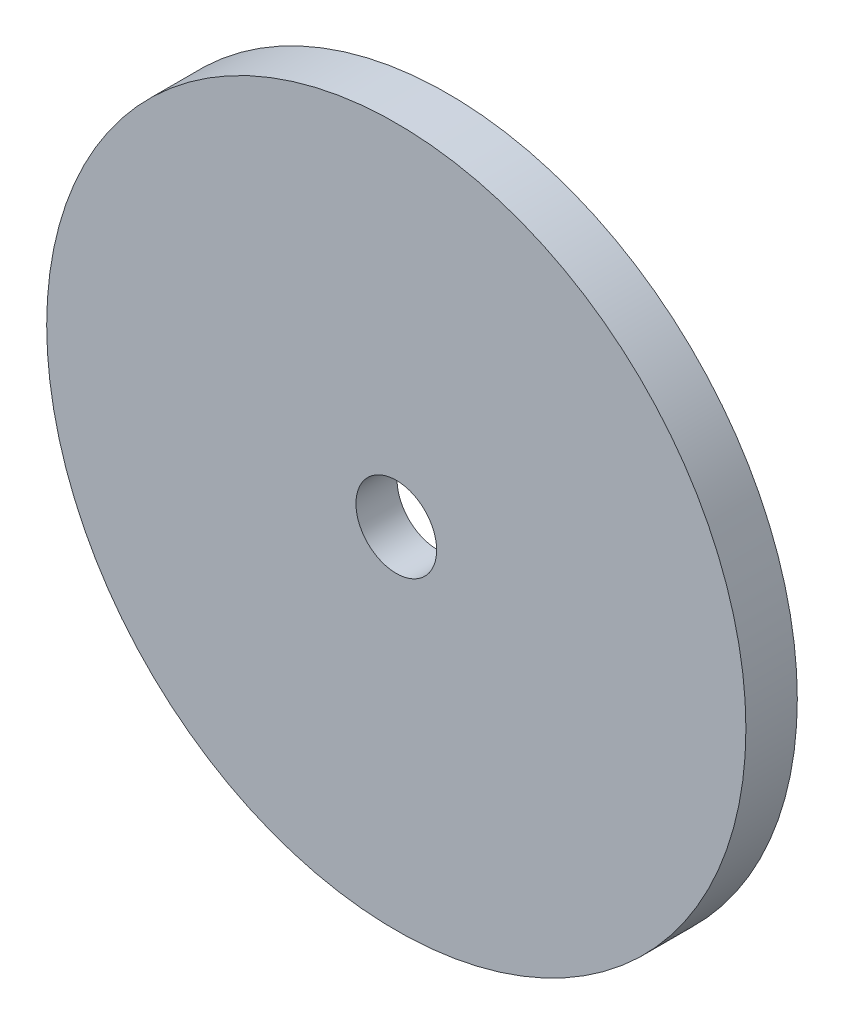
SolidWorks part; units mm, degrees
ref_plane "Front Plane" through (0, 0, 0) normal (0, 0, 1) x (1, 0, 0)
ref_plane "Top Plane" through (0, 0, 0) normal (0, 1, 0) x (1, 0, 0)
ref_plane "Right Plane" through (0, 0, 0) normal (1, 0, 0) x (0, 0, -1)
sketch "Sketch3" plane through (0, 0, 0) normal (0, 0, 1) x (1, 0, 0)
  circle A1 centre (9.62, 10) radius 34
  circle A2 centre (9.62, 10) radius 10.9
  circle A3 centre (9.62, 10) radius 10.9
  dimension "D2" = 68
  dimension "D1" = 0.5
extrude "Boss-Extrude2" add sketch "Sketch3" against normal blind 1
sketch "Sketch4" plane through (0, 0, 0) normal (0, 0, 1) x (1, 0, 0)
  circle A1 centre (9.62, 10) radius 34
  circle A2 centre (9.62, 10) radius 3.925
  circle A3 centre (9.62, 10) radius 3.925
  dimension "D1" = 1
extrude "Boss-Extrude3" add sketch "Sketch4" along normal blind 4
